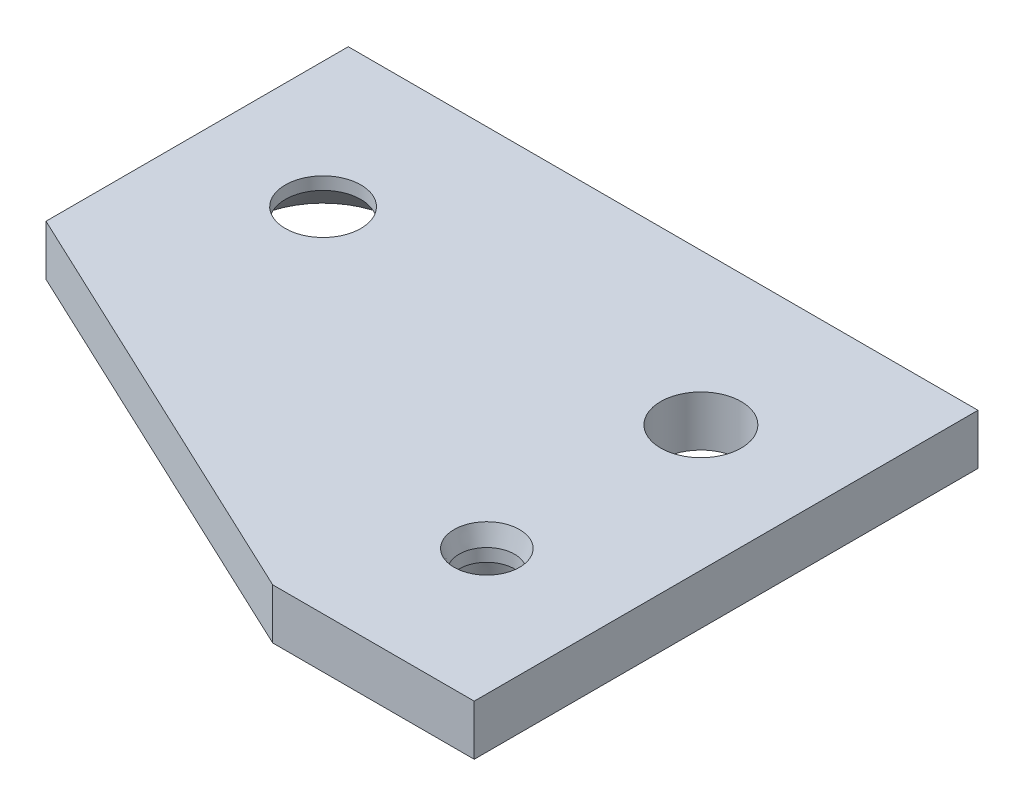
SolidWorks part; units mm, degrees
material "6061 Alloy"
ref_plane "Front Plane" through (0, 0, 0) normal (0, 0, 1) x (1, 0, 0)
ref_plane "Top Plane" through (0, 0, 0) normal (0, 1, 0) x (1, 0, 0)
ref_plane "Right Plane" through (0, 0, 0) normal (1, 0, 0) x (0, 0, -1)
sketch "Sketch1" plane through (0, 0, 0) normal (0, 1, 0) x (1, 0, 0)
  line L0 (0, 0) -> (-15, 0) construction
  line L1 (-20, 6) -> (5, 6)
  line L2 (-20, 6) -> (-20, -6)
  line L3 (-3, -14) -> (5, -14)
  line L4 (5, 6) -> (5, -14)
  line L5 (-3, -14) -> (-20, -6)
  circle A0 centre (0, 0) radius 1.6
  circle A1 centre (-15, 0) radius 1.5
  circle A4 centre (0, -8.5) radius 1.1
  dimension "D1" = 3.2
  dimension "D2" = 3
  dimension "D8" = 2.2
  dimension "D3" = 15
  dimension "D4" = 5
  dimension "D5" = 5
  dimension "D6" = 6
  dimension "D7" = 8.5
  dimension "D10" = 20
  dimension "D11" = 12
  dimension "D12" = 8
extrude "Extrude1" add sketch "Sketch1" along normal blind 2
chamfer "Chamfer1" distance 1.5 angle 45 1 edges at (-15, 0, 1.5)
chamfer "Chamfer2" distance 0.2 angle 75 2 edges at (0, 0, 9.6) (0, 2, 9.6)
